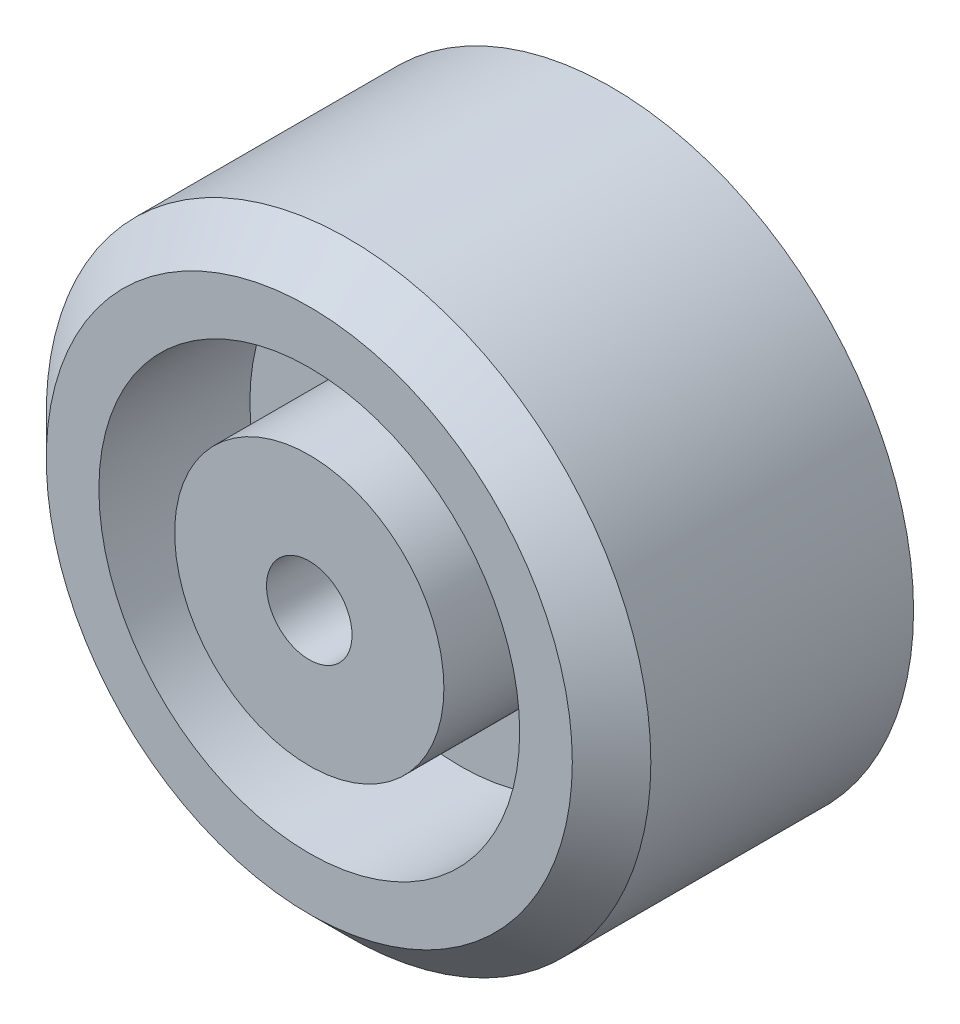
SolidWorks part; units mm, degrees
ref_plane "Alzado" through (0, 0, 0) normal (0, 0, 1) x (1, 0, 0)
ref_plane "Planta" through (0, 0, 0) normal (0, 1, 0) x (1, 0, 0)
ref_plane "Vista lateral" through (0, 0, 0) normal (1, 0, 0) x (0, 0, -1)
sketch "Croquis1" plane through (0, 0, 0) normal (0, 0, 1) x (1, 0, 0)
  circle A0 centre (-9.1007, 10.6632) radius 10.0098
  circle A1 centre (-9.1007, 10.6632) radius 1.4154
extrude "Saliente-Extruir1" add sketch "Croquis1" along normal blind 10
sketch "Croquis4" plane through (0, 0, 10) normal (0, 0, 1) x (1, 0, 0)
  circle A0 centre (-9.1007, 10.6632) radius 6.967
  circle A1 centre (-9.1007, 10.6632) radius 4.4575
extrude "Cortar-Extruir2" cut sketch "Croquis4" against normal blind 5
chamfer "Chaflán5" distance 1.3 angle 45 1 edges at (0.9091, 10.6632, 10)
